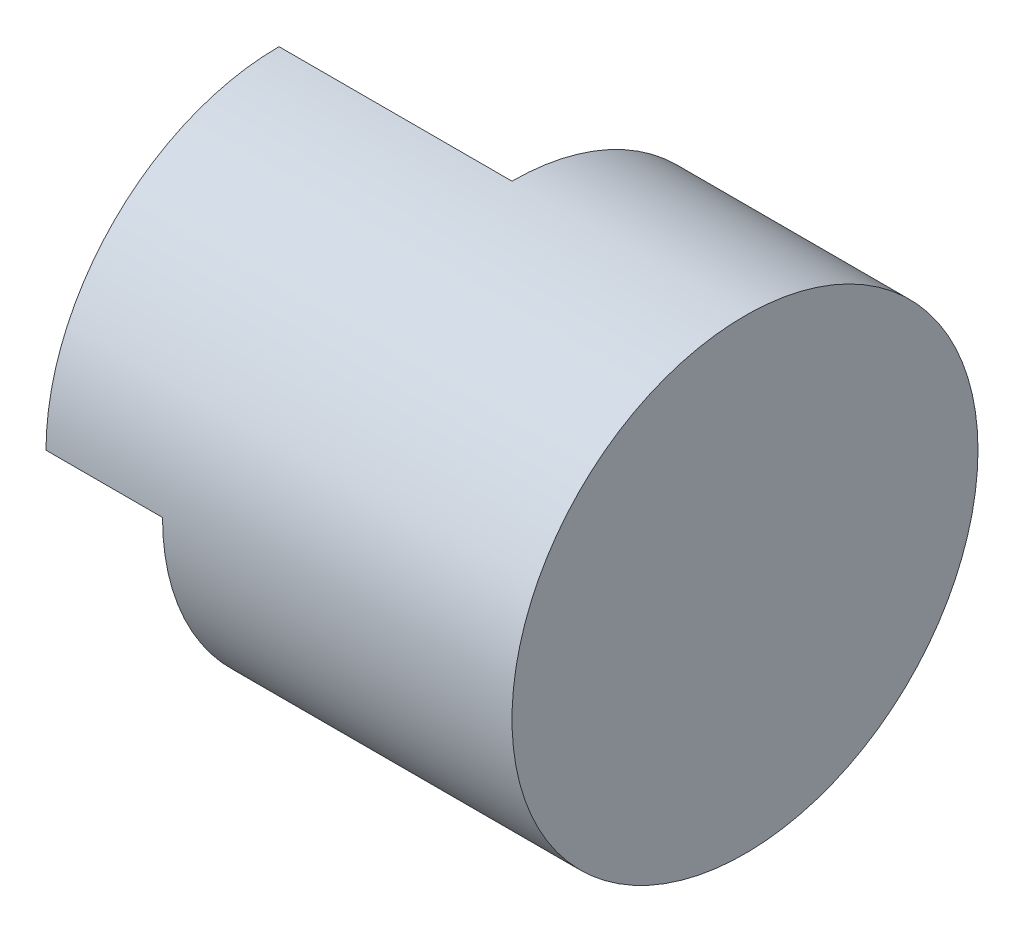
SolidWorks part; units mm, degrees
ref_plane "Front" through (0, 0, 0) normal (0, 0, 1) x (1, 0, 0)
ref_plane "Top" through (0, 0, 0) normal (0, 1, 0) x (1, 0, 0)
ref_plane "Right" through (0, 0, 0) normal (1, 0, 0) x (0, 0, -1)
sketch "Sketch1" plane through (0, 0, 0) normal (1, 0, 0) x (0, 0, -1)
  circle A0 centre (0, 0) radius 2
  dimension "D1" = 4
extrude "Boss-Extrude1" add sketch "Sketch1" along normal mid plane 4
sketch "Sketch2" plane through (0, 0, 0) normal (0, 0, 1) x (1, 0, 0)
  line L0 (0, 2) -> (0, 0)
  line L1 (2, 2) -> (-2, 2) construction
  line L2 (0, 0) -> (-2, 0)
  line L3 (-2, 2) -> (-2, -2) construction
  line L4 (-2, 0) -> (-2, 2)
  line L5 (-2, 2) -> (0, 2)
extrude "Cut-Extrude1" cut sketch "Sketch2" against normal blind 4
sketch "Sketch3" plane through (-2, 0, 0) normal (-1, 0, 0) x (0, 0, 1)
  line L1 (-2, 0) -> (2.2952, 0)
  line L2 (-2, 0) -> (-2, -2.1328)
  line L3 (-2, -2.1328) -> (2.2952, -2.1328)
  line L4 (2.2952, 0) -> (2.2952, -2.1328)
extrude "Cut-Extrude2" cut sketch "Sketch3" against normal blind 1
